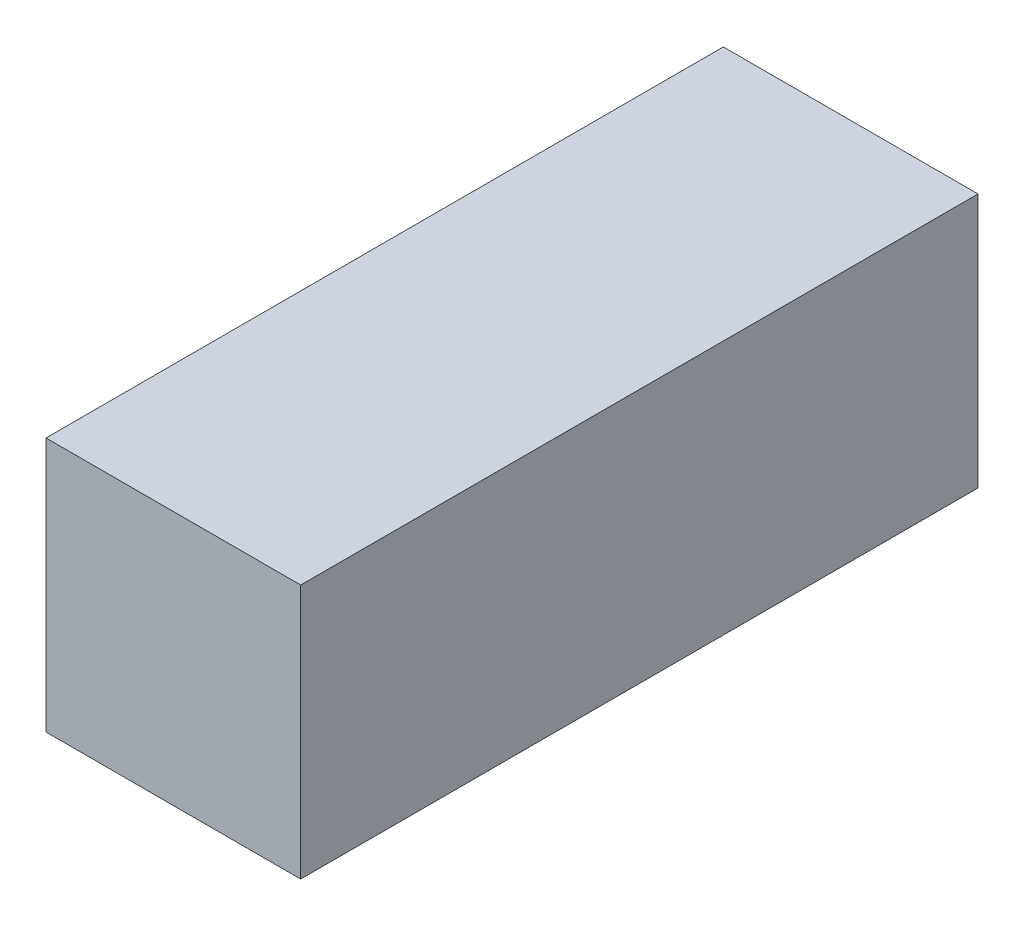
SolidWorks part; units mm, degrees
ref_plane "Front Plane" through (0, 0, 0) normal (0, 0, 1) x (1, 0, 0)
ref_plane "Top Plane" through (0, 0, 0) normal (0, 1, 0) x (1, 0, 0)
ref_plane "Right Plane" through (0, 0, 0) normal (1, 0, 0) x (0, 0, -1)
sketch "Sketch1" plane through (0, 0, 0) normal (0, 0, 1) x (1, 0, 0)
  line L1 (0, 0) -> (4.7752, 0)
  line L2 (0, 0) -> (0, 4.7752)
  line L3 (0, 4.7752) -> (4.7752, 4.7752)
  line L4 (4.7752, 0) -> (4.7752, 4.7752)
  dimension "D1" = 4.7752
  dimension "D2" = 4.7752
extrude "Boss-Extrude1" add sketch "Sketch1" along normal blind 12.7
